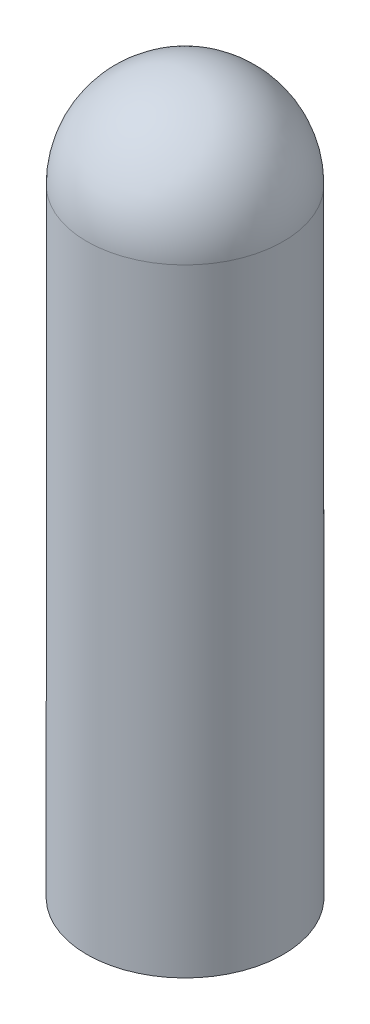
SolidWorks part; units mm, degrees
material "Rubber"
ref_plane "Front Plane" through (0, 0, 0) normal (0, 0, 1) x (1, 0, 0)
ref_plane "Top Plane" through (0, 0, 0) normal (0, 1, 0) x (1, 0, 0)
ref_plane "Right Plane" through (0, 0, 0) normal (1, 0, 0) x (0, 0, -1)
sketch "Sketch1" plane through (0, 0, 0) normal (0, 0, 1) x (1, 0, 0)
  line L0 (-4.3561, 0) -> (-4.3561, 27.3939)
  line L1 (0, 0) -> (0, -6.35) construction
  line L2 (0, -55) -> (0, 55) construction
  line L3 (-4.3561, 0) -> (0, 0)
  line L4 (0, 0) -> (0, 31.75)
  arc A0 (-4.3561, 27.3939) -> (0, 31.75) centre (0, 27.3939) cw
  dimension "D1" = 31.75
  dimension "D2" = 8.7122
  dimension "D3" = 6.35
  dimension "D4" = 27.3939
revolve "Revolve1" add sketch "Sketch1" angle 360 about L1
sketch "Sketch2" plane through (0, 0, 0) normal (0, -1, 0) x (1, 0, 0)
  circle A0 centre (0, 0) radius 3.9751
  circle A1 centre (0, 0) radius 4.3561 construction
  dimension "D1" = 0.381
  dimension "D2" = 7.9502
extrude "Cut-Extrude1" cut sketch "Sketch2" against normal blind 27.7749
